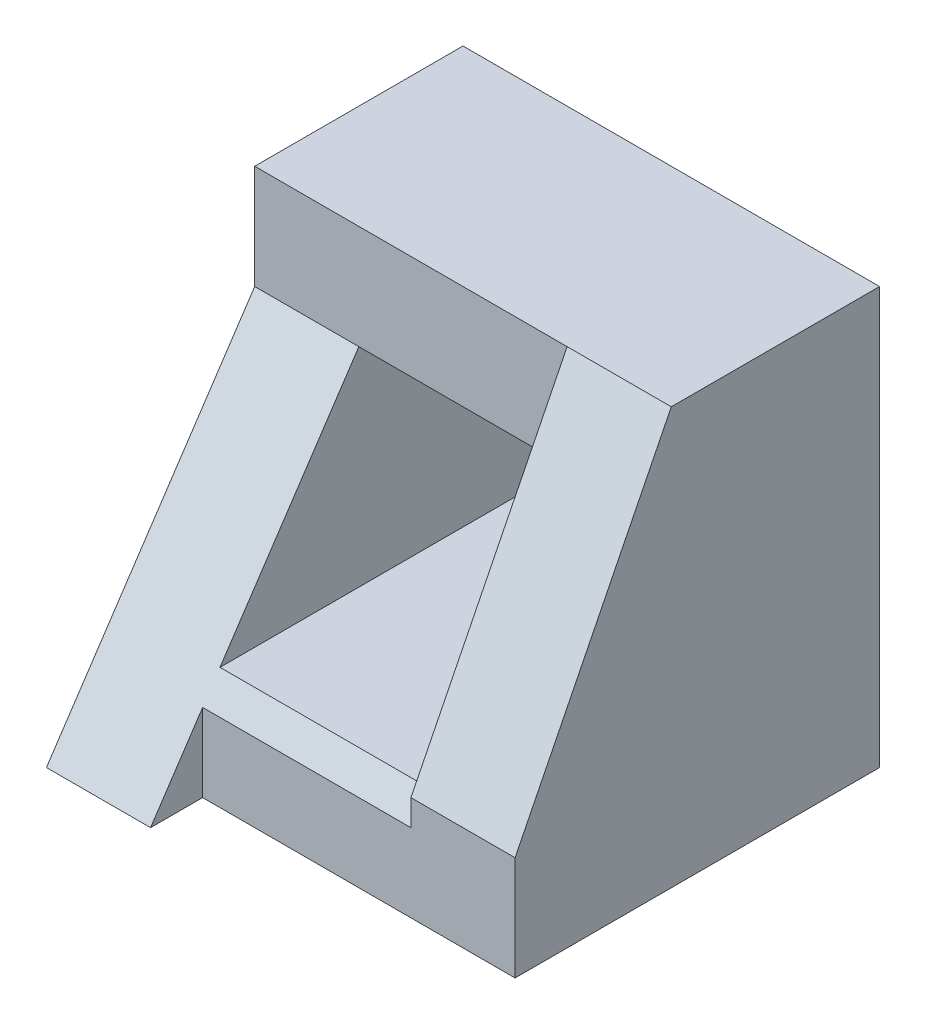
SolidWorks part; units mm, degrees
ref_plane "Front Plane" through (0, 0, 0) normal (0, 0, 1) x (1, 0, 0)
ref_plane "Top Plane" through (0, 0, 0) normal (0, 1, 0) x (1, 0, 0)
ref_plane "Right Plane" through (0, 0, 0) normal (1, 0, 0) x (0, 0, -1)
sketch "Sketch1" plane through (0, 0, 0) normal (0, 0, 1) x (1, 0, 0)
  line L1 (0, 0) -> (4, 0)
  line L2 (0, 0) -> (0, 4)
  line L3 (0, 4) -> (4, 4)
  line L4 (4, 0) -> (4, 4)
  line L5 (1, 1) -> (3, 1)
  line L6 (1, 1) -> (1, 3)
  line L7 (1, 3) -> (3, 3)
  line L8 (3, 1) -> (3, 3)
  dimension "D1" = 4
  dimension "D2" = 2
  dimension "D3" = 1
  dimension "D4" = 4
  dimension "D5" = 2
  dimension "D6" = 1
extrude "Boss-Extrude1" add sketch "Sketch1" along normal blind 4
sketch "Sketch2" plane through (4, 0, 0) normal (1, 0, 0) x (0, 0, -1)
  line L0 (-2, 4) -> (-4, 0)
  line L1 (-4, 4) -> (0, 4) construction
  line L2 (-4, 0) -> (-4, 4)
  line L3 (-4, 4) -> (-2, 4)
extrude "Cut-Extrude1" cut sketch "Sketch2" against normal blind 4
sketch "Sketch3" plane through (0, 0, 0) normal (-1, 0, 0) x (0, 0, 1)
  line L0 (2, 4) -> (2, 3)
  line L1 (2, 3) -> (2.5, 3)
  line L2 (4, 0) -> (2, 4) construction
  line L3 (2.5, 3) -> (2, 4)
  dimension "D1" = 1
extrude "Cut-Extrude2" cut sketch "Sketch3" against normal blind 3
sketch "Sketch4" plane through (0, 0, 0) normal (-1, 0, 0) x (0, 0, 1)
  line L0 (2, 3) -> (4, 0)
  line L1 (4, 0) -> (4, 3.2228)
  line L2 (4, 3.2228) -> (2, 3)
  point P5 (0, 0)
extrude "Cut-Extrude3" cut sketch "Sketch4" against normal blind 3
sketch "Sketch6" plane through (4, 0, 0) normal (1, 0, 0) x (0, 0, -1)
  line L0 (-3.5, 0) -> (-3.5, 1)
  line L1 (-4, 0) -> (0, 0) construction
  line L2 (-4, 0) -> (-2, 4) construction
  line L3 (-3.5, 1) -> (-4, 0)
  line L4 (-4, 0) -> (-3.5, 0)
  dimension "D1" = 1
extrude "Cut-Extrude5" cut sketch "Sketch6" against normal blind 3
